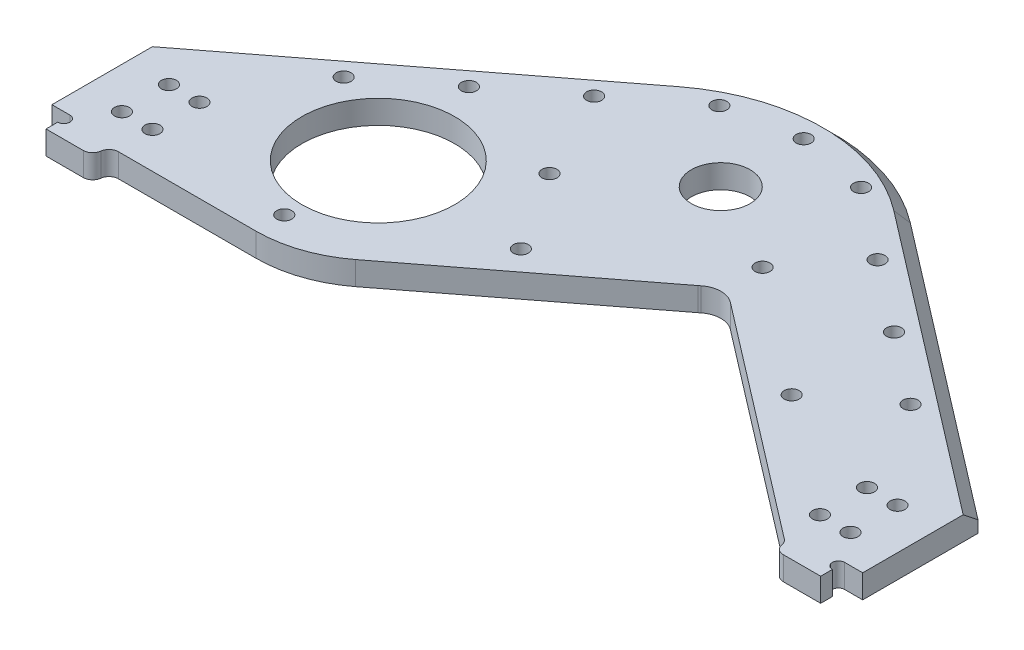
SolidWorks part; units mm, degrees
material "Alum Plate"
ref_plane "Front Plane" through (0, 0, 0) normal (0, 0, 1) x (1, 0, 0)
ref_plane "Top Plane" through (0, 0, 0) normal (0, 1, 0) x (1, 0, 0)
ref_plane "Right Plane" through (0, 0, 0) normal (1, 0, 0) x (0, 0, -1)
sketch "Top Layout" plane through (0, 0, 0) normal (0, 1, 0) x (1, 0, 0)
  line L0 (-114.046, -123.825) -> (-104.775, -123.825) construction
  line L1 (-104.775, -142.875) -> (-101.6, -142.875)
  line L2 (-104.775, -142.875) -> (-104.775, -104.775)
  line L3 (-104.775, -104.775) -> (-101.6, -104.775)
  line L4 (-101.6, -142.875) -> (-101.6, -104.775)
  line L5 (-104.775, -142.875) -> (-101.6, -104.775) construction
  line L6 (-104.775, -104.775) -> (-101.6, -142.875) construction
  line L7 (-19.05, -105.8164) -> (-101.6, -105.8164)
  line L8 (-19.05, -105.8164) -> (-19.05, -141.8336)
  line L9 (-19.05, -141.8336) -> (-101.6, -141.8336)
  line L10 (-101.6, -105.8164) -> (-101.6, -141.8336)
  line L11 (-19.05, -105.8164) -> (-101.6, -141.8336) construction
  line L12 (-19.05, -141.8336) -> (-101.6, -105.8164) construction
  line L13 (-133.096, -85.725) -> (-114.046, -85.725)
  line L14 (-133.096, -85.725) -> (-133.096, -161.925)
  line L15 (-133.096, -161.925) -> (-114.046, -161.925)
  line L16 (-114.046, -85.725) -> (-114.046, -161.925)
  line L17 (-133.096, -85.725) -> (-114.046, -161.925) construction
  line L18 (-133.096, -161.925) -> (-114.046, -85.725) construction
  line L19 (-104.775, -123.825) -> (0, -123.825) construction
  line L20 (0, -123.825) -> (0, 0) construction
  line L21 (-52.3528, -40.1717) -> (0, 0) construction
  line L22 (-70.6449, -16.3328) -> (-18.2922, 23.8388)
  line L23 (-34.0606, -64.0105) -> (18.2922, -23.8388)
  line L24 (-30.9251, 40.3023) -> (-122.2248, -29.7544)
  line L25 (-153.9748, -53.975) -> (-153.9748, -123.825)
  line L26 (-109.5248, -162.052) -> (109.5248, -162.052)
  line L27 (0, -162.052) -> (0, -123.825) construction
  line L28 (-109.5248, -162.052) -> (-109.5248, -20.0093) construction
  line L29 (-104.775, -142.875) -> (-104.775, -152.527)
  line L30 (-104.775, -152.527) -> (104.775, -152.527)
  line L31 (104.775, -104.775) -> (101.6, -104.775)
  line L32 (-144.4498, -73.025) -> (-109.5248, -73.025)
  line L33 (-144.4498, -73.025) -> (-144.4498, -123.825)
  line L34 (-144.4498, -123.825) -> (-109.5248, -123.825) construction
  line L35 (-109.5248, -73.025) -> (-109.5248, -162.052)
  line L36 (-144.4498, -73.025) -> (-109.5248, -123.825) construction
  line L37 (-144.4498, -123.825) -> (-109.5248, -73.025) construction
  line L38 (101.6, -142.875) -> (101.6, -104.775)
  line L39 (104.775, -142.875) -> (101.6, -142.875)
  line L40 (104.775, -142.875) -> (104.775, -104.775)
  line L41 (104.775, -142.875) -> (104.775, -152.527)
  line L42 (109.5248, -162.052) -> (109.5248, -20.0093) construction
  line L43 (30.9251, 40.3023) -> (122.2248, -29.7544)
  line L45 (19.05, -141.8336) -> (101.6, -141.8336)
  line L46 (101.6, -105.8164) -> (101.6, -141.8336)
  line L47 (19.05, -105.8164) -> (101.6, -105.8164)
  line L48 (19.05, -105.8164) -> (19.05, -141.8336)
  line L49 (133.096, -161.925) -> (114.046, -161.925)
  line L50 (114.046, -85.725) -> (114.046, -161.925)
  line L51 (133.096, -85.725) -> (114.046, -85.725)
  line L52 (133.096, -85.725) -> (133.096, -161.925)
  line L53 (144.4498, -123.825) -> (109.5248, -123.825) construction
  line L54 (109.5248, -73.025) -> (109.5248, -162.052)
  line L55 (144.4498, -73.025) -> (109.5248, -73.025)
  line L56 (144.4498, -73.025) -> (144.4498, -123.825)
  line L57 (-109.5248, -123.825) -> (-109.5248, -162.052) construction
  line L62 (-153.9748, -53.975) -> (-122.2248, -53.975)
  line L63 (-122.2248, -53.975) -> (-122.2248, -29.7544)
  line L64 (-144.4498, -123.825) -> (-153.9748, -123.825)
  line L65 (153.9748, -53.975) -> (153.9748, -123.825)
  line L66 (109.5248, -123.825) -> (109.5248, -162.052) construction
  line L67 (144.4498, -123.825) -> (153.9748, -123.825)
  line L68 (122.2248, -29.7544) -> (122.2248, -53.975)
  line L73 (-104.775, -104.775) -> (-104.775, -16.3647) construction
  line L74 (-95.25, -162.052) -> (-95.25, -9.0559) construction
  line L75 (-109.5248, -162.052) -> (-109.5248, -123.825) construction
  line L76 (109.5248, -162.052) -> (109.5248, -123.825) construction
  line L77 (122.2248, -53.975) -> (153.9748, -53.975)
  line L83 (104.775, -155.5496) -> (-104.775, -155.5496) construction
  line L88 (95.25, -162.052) -> (95.25, -9.0559) construction
  line L89 (104.775, -104.775) -> (104.775, -16.3647) construction
  line L92 (-104.775, -152.527) -> (-104.775, -162.052) construction
  line L93 (-14.605, -76.327) -> (14.605, -76.327)
  line L94 (-14.605, -76.327) -> (-14.605, -152.527)
  line L95 (-14.605, -152.527) -> (14.605, -152.527)
  line L96 (14.605, -76.327) -> (14.605, -152.527)
  line L97 (-14.605, -76.327) -> (14.605, -152.527) construction
  line L98 (-14.605, -152.527) -> (14.605, -76.327) construction
  line L99 (104.775, -152.527) -> (104.775, -162.052) construction
  line L100 (-19.05, -105.8164) -> (0, -105.8164) construction
  line L107 (0, -105.8164) -> (19.05, -105.8164) construction
  line L108 (104.775, -123.825) -> (114.046, -123.825) construction
  circle A0 centre (0, 0) radius 114.3
  circle A1 centre (0, 0) radius 7.9375
  circle A2 centre (-52.3528, -40.1717) radius 17.8
  circle A3 centre (0, 0) radius 30.0482
  circle A4 centre (-52.3528, -40.1717) radius 30.0482
  arc A5 (-30.9251, 40.3023) -> (30.9251, 40.3023) centre (0, 0) cw
  point P2 (-103.1875, -123.825)
  point P7 (-60.325, -123.825)
  point P12 (-123.571, -123.825)
  point P30 (-126.9873, -98.425)
  point P35 (0, -114.427)
  point P53 (0, -152.527)
  dimension "D1" = 35.6
  dimension "D2" = 15.875
  dimension "D3" = 228.6
  dimension "D11" = 60.0964
  dimension "D12" = 50.8
  dimension "D14" = 52.5
  dimension "D4" = 3.175
  dimension "D5" = 19.05
  dimension "D6" = 76.2
  dimension "D7" = 82.55
  dimension "D8" = 38.1
  dimension "D9" = 104.775
  dimension "D10" = 18.0086
  dimension "D13" = 9.525
  dimension "D15" = 4.7498
  dimension "D16" = 9.525
  dimension "D17" = 9.652
  dimension "D18" = 50.8
  dimension "D19" = 12.446
  dimension "D20" = 65.9892
  dimension "D21" = 19.05
  dimension "D22" = 34.925
  dimension "D23" = 123.825
  dimension "D24" = 12.7
  dimension "D25" = 9.525
  dimension "D26" = 29.21
  dimension "D27" = 76.2
  dimension "D28" = 3.0226
sketch "Side Layout" plane through (0, 0, 0) normal (1, 0, 0) x (0, 0, -1)
  line L0 (0, -38.1) -> (0, 33.7344) construction
  line L1 (-114.3, -20.955) -> (114.3, -20.955)
  line L2 (-114.3, -20.955) -> (-114.3, -33.655)
  line L3 (-114.3, -33.655) -> (114.3, -33.655)
  line L4 (114.3, -20.955) -> (114.3, -33.655)
  line L5 (-114.3, -20.955) -> (114.3, -33.655) construction
  line L6 (-114.3, -33.655) -> (114.3, -20.955) construction
  line L7 (-9.525, -32.9406) -> (9.525, -32.9406)
  line L8 (-9.525, -32.9406) -> (-9.525, -38.1)
  line L9 (-9.525, -38.1) -> (9.525, -38.1)
  line L10 (9.525, -32.9406) -> (9.525, -38.1)
  line L11 (-9.525, -32.9406) -> (9.525, -38.1) construction
  line L12 (-9.525, -38.1) -> (9.525, -32.9406) construction
  line L13 (-11.9126, -29.3338) -> (11.9126, -29.3338)
  line L14 (-11.9126, -29.3338) -> (-11.9126, -32.9406)
  line L15 (-11.9126, -32.9406) -> (11.9126, -32.9406)
  line L16 (11.9126, -29.3338) -> (11.9126, -32.9406)
  line L17 (-11.9126, -29.3338) -> (11.9126, -32.9406) construction
  line L18 (-11.9126, -32.9406) -> (11.9126, -29.3338) construction
  line L19 (-6.35, -32.9406) -> (6.35, -32.9406)
  line L20 (-6.35, -32.9406) -> (-6.35, 33.7344)
  line L21 (-6.35, 33.7344) -> (6.35, 33.7344)
  line L22 (6.35, -32.9406) -> (6.35, 33.7344)
  line L23 (-6.35, -32.9406) -> (6.35, 33.7344) construction
  line L24 (-6.35, 33.7344) -> (6.35, -32.9406) construction
  line L25 (-162.052, 0) -> (-123.825, 0) construction
  line L26 (114.3, -33.655) -> (114.3, 0) construction
  line L27 (-142.875, 19.05) -> (-104.775, 19.05)
  line L28 (-40.1717, -9.525) -> (-40.1717, 5.4) construction
  line L29 (-142.875, 19.05) -> (-142.875, -19.05)
  line L30 (-142.875, -19.05) -> (-104.775, -19.05)
  line L31 (-104.775, 19.05) -> (-104.775, -19.05)
  line L32 (-142.875, 19.05) -> (-104.775, -19.05) construction
  line L33 (-142.875, -19.05) -> (-104.775, 19.05) construction
  line L34 (-130.175, -38.1) -> (-117.9516, -38.1) construction
  line L35 (-57.9717, -14.6) -> (-22.3717, -14.6)
  line L36 (-30.0482, -2.794) -> (30.0482, -2.794)
  line L37 (-30.0482, -2.794) -> (-30.0482, -20.955)
  line L38 (-30.0482, -20.955) -> (30.0482, -20.955)
  line L39 (30.0482, -2.794) -> (30.0482, -20.955)
  line L40 (-30.0482, -2.794) -> (30.0482, -20.955) construction
  line L41 (-30.0482, -20.955) -> (30.0482, -2.794) construction
  line L42 (-30.0482, -2.794) -> (-30.0482, 0) construction
  line L43 (-123.825, 0) -> (0, 0) construction
  line L44 (-57.9717, -14.6) -> (-57.9717, 25.4)
  line L45 (-57.9717, 25.4) -> (-22.3717, 25.4)
  line L46 (-22.3717, -14.6) -> (-22.3717, 25.4)
  line L47 (-19.05, 0) -> (19.05, 0)
  line L48 (-19.05, 0) -> (-19.05, -1.9812)
  line L49 (-19.05, -1.9812) -> (19.05, -1.9812)
  line L50 (19.05, 0) -> (19.05, -1.9812)
  line L51 (-19.05, 0) -> (19.05, -1.9812) construction
  line L52 (-19.05, -1.9812) -> (19.05, 0) construction
  line L53 (-70.2199, -3.175) -> (-10.1235, -3.175)
  line L54 (-70.2199, -3.175) -> (-70.2199, -15.875)
  line L55 (-70.2199, -15.875) -> (-10.1235, -15.875)
  line L56 (-10.1235, -3.175) -> (-10.1235, -15.875)
  line L57 (-70.2199, -3.175) -> (-10.1235, -15.875) construction
  line L58 (-70.2199, -15.875) -> (-10.1235, -3.175) construction
  line L59 (-40.1717, -9.525) -> (-40.1717, 0) construction
  line L60 (-57.9717, -14.6) -> (-22.3717, 25.4) construction
  line L61 (-57.9717, 25.4) -> (-22.3717, -14.6) construction
  line L62 (-22.3717, 0) -> (-57.9717, 0) construction
  line L63 (-137.8162, 0) -> (-123.825, -13.9912) construction
  line L64 (-139.065, 15.24) -> (-108.585, 15.24) construction
  line L65 (-139.065, 15.24) -> (-139.065, -15.24) construction
  line L66 (-139.065, -15.24) -> (-108.585, -15.24) construction
  line L67 (-108.585, 15.24) -> (-108.585, -15.24) construction
  line L68 (-139.065, 15.24) -> (-108.585, -15.24) construction
  line L69 (-139.065, -15.24) -> (-108.585, 15.24) construction
  line L70 (-137.8162, 0) -> (-123.825, 13.9912) construction
  line L71 (-123.825, -13.9912) -> (-109.8338, 0) construction
  line L72 (-123.825, 13.9912) -> (-109.8338, 0) construction
  line L73 (-137.8162, 0) -> (-109.8338, 0) construction
  line L74 (-123.825, -13.9912) -> (-123.825, 13.9912) construction
  line L75 (-6.35, 17.8594) -> (6.35, 17.8594)
  line L76 (114.3, 0) -> (-114.3, 0) construction
  line L77 (-22.3717, 19.05) -> (-6.35, 19.05) construction
  line L78 (-123.825, 38.1) -> (-97.9206, 38.1) construction
  line L79 (-19.05, -3.5814) -> (19.05, -3.5814)
  line L80 (-19.05, -3.5814) -> (-19.05, -1.9812)
  line L81 (-19.05, -1.9812) -> (19.05, -1.9812)
  line L82 (19.05, -3.5814) -> (19.05, -1.9812)
  line L83 (-19.05, -3.5814) -> (19.05, -1.9812) construction
  line L84 (-19.05, -1.9812) -> (19.05, -3.5814) construction
  line L85 (-8.7376, -16.7608) -> (8.7376, -16.7608)
  line L86 (-8.7376, -16.7608) -> (-8.7376, -29.3338)
  line L87 (-8.7376, -29.3338) -> (8.7376, -29.3338)
  line L88 (8.7376, -16.7608) -> (8.7376, -29.3338)
  line L89 (-8.7376, -16.7608) -> (8.7376, -29.3338) construction
  line L90 (-8.7376, -29.3338) -> (8.7376, -16.7608) construction
  line L91 (-8.7376, -3.5814) -> (8.7376, -3.5814)
  line L92 (-8.7376, -3.5814) -> (-8.7376, -16.1544)
  line L93 (-8.7376, -16.1544) -> (8.7376, -16.1544)
  line L94 (8.7376, -3.5814) -> (8.7376, -16.1544)
  line L95 (-8.7376, -3.5814) -> (8.7376, -16.1544) construction
  line L96 (-8.7376, -16.1544) -> (8.7376, -3.5814) construction
  circle A0 centre (-123.825, 0) radius 18.0086
  circle A1 centre (-123.825, 0) radius 38.1
  circle A2 centre (-139.065, 15.24) radius 1.905
  circle A3 centre (-108.585, 15.24) radius 1.905
  circle A4 centre (-108.585, -15.24) radius 1.905
  circle A5 centre (-139.065, -15.24) radius 1.905
  circle A6 centre (-137.8162, 0) radius 1.6002
  circle A7 centre (-123.825, 13.9912) radius 1.6002
  circle A8 centre (-109.8338, 0) radius 1.6002
  circle A9 centre (-123.825, -13.9912) radius 1.6002
  point P0 (0, -27.305)
  point P6 (0, -31.1372)
  point P7 (0, -35.5203)
  point P21 (0, 0.3969)
  point P32 (0, -11.8745)
  point P43 (0, -0.9906)
  point P55 (-40.1717, -9.525)
  point P72 (-40.1717, 5.4)
  point P88 (0, -23.0473)
  point P93 (0, -2.7813)
  point P102 (0, -9.8679)
  dimension "D17" = 3.81
  dimension "D18" = 3.2004
  dimension "D1" = 12.7
  dimension "D2" = 5.1594
  dimension "D3" = 19.05
  dimension "D4" = 3.6068
  dimension "D5" = 23.8252
  dimension "D6" = 12.7
  dimension "D7" = 18.161
  dimension "D8" = 1.9812
  dimension "D9" = 12.7
  dimension "D10" = 40
  dimension "D11" = 25.4
  dimension "D12" = 50.8
  dimension "D13" = 41.275
  dimension "D14" = 30.48
  dimension "D15" = 4.445
  dimension "D16" = 19.7866
  dimension "D19" = 15.875
  dimension "D20" = 6.35
  dimension "D21" = 38.1
  dimension "D22" = 1.6002
  dimension "D23" = 38.1
  dimension "D24" = 17.4752
  dimension "D25" = 12.573
ref_plane "Plane1" through (0, 25.4, 0) normal (0, 1, 0) x (1, 0, 0)
sketch "Sketch3" plane through (0, 25.4, 0) normal (0, 1, 0) x (1, 0, 0)
  line L0 (-104.775, -36.3747) -> (-30.9251, 20.2924)
  line L1 (-104.775, -104.775) -> (-104.775, -16.3647) construction
  line L2 (0, -200130.175) -> (0, 199882.0484) construction
  line L3 (-30.9251, 40.3023) -> (-122.2248, -29.7544) construction
  line L5 (-104.775, -36.3747) -> (-104.775, -77.6497)
  line L6 (-92.075, -77.6497) -> (-104.775, -77.6497)
  line L7 (30.9251, 20.2924) -> (104.775, -36.3747)
  line L8 (104.775, -77.6497) -> (92.075, -77.6497)
  line L9 (104.775, -36.3747) -> (104.775, -77.6497)
  line L11 (104.775, -104.775) -> (104.775, -16.3647) construction
  line L12 (30.9251, 40.3023) -> (122.2248, -29.7544) construction
  line L13 (92.075, -74.6536) -> (24.1423, -22.5271)
  line L14 (-32.2514, -66.3682) -> (20.1013, -26.1965)
  line L15 (-30.9251, 20.2924) -> (0, 44.022)
  line L16 (0, 44.022) -> (30.9251, 20.2924)
  line L17 (-92.075, -77.6497) -> (-92.075, -73.1917)
  line L19 (-92.075, -73.1917) -> (-52.3528, -73.1917)
  line L20 (92.075, -74.6536) -> (92.075, -77.6497)
  circle A0 centre (-52.3528, -40.1717) radius 17.8 construction
  circle A1 centre (-52.3528, -40.1717) radius 17.8
  circle A2 centre (0, 0) radius 7.9375
  circle A3 centre (0, 0) radius 7.9375 construction
  arc A4 (-52.3528, -73.1917) -> (-32.2514, -66.3682) centre (-52.3528, -40.1717) ccw
  arc A5 (20.1013, -26.1965) -> (24.1423, -22.5271) centre (0, 0) ccw
  arc A6 (30.9251, 20.2924) -> (-30.9251, 20.2924) centre (0, -20.01) ccw construction
  point P28 (0, 44.022)
  dimension "D1" = 33.02
  dimension "D5" = 50.8
  dimension "D2" = 41.275
  dimension "D3" = 34.925
  dimension "D4" = 12.7
  dimension "D6" = 38.1
extrude "Boss-Extrude1" add sketch "Sketch3" against normal blind 6.35
sketch "Sketch7" plane through (0, 25.4, 0) normal (0, 1, 0) x (1, 0, 0)
  circle A0 centre (-52.3528, -40.1717) radius 20.6375
  dimension "D1" = 41.275
extrude "Cut-Extrude1" cut sketch "Sketch7" against normal through all
sketch "Sketch8" plane through (0, 25.4, 0) normal (0, 1, 0) x (1, 0, 0)
  line L0 (-109.5248, -162.052) -> (-109.5248, -20.0093) construction
  line L1 (-104.775, -77.6497) -> (-109.5248, -77.6497)
  line L2 (-104.775, -77.6497) -> (-104.775, -36.3747)
  line L3 (-104.775, -36.3747) -> (-109.5248, -36.3747)
  line L4 (-109.5248, -77.6497) -> (-109.5248, -36.3747)
  line L5 (-104.775, -77.6497) -> (-109.5248, -36.3747) construction
  line L6 (-104.775, -36.3747) -> (-109.5248, -77.6497) construction
  line L7 (104.775, -77.6497) -> (109.5248, -77.6497)
  line L8 (104.775, -77.6497) -> (104.775, -36.3747)
  line L9 (104.775, -36.3747) -> (109.5248, -36.3747)
  line L10 (109.5248, -77.6497) -> (109.5248, -36.3747)
  line L11 (104.775, -77.6497) -> (109.5248, -36.3747) construction
  line L12 (104.775, -36.3747) -> (109.5248, -77.6497) construction
  point P4 (-107.1499, -57.0122)
  point P10 (107.1499, -57.0122)
extrude "Boss-Extrude4" add sketch "Sketch8" against normal through all
sketch "Sketch10" plane through (0, 25.4, 0) normal (0, 1, 0) x (1, 0, 0)
  line L0 (0, 33.4567) -> (0, 30.79) construction
  line L1 (-5.1026, 40.1066) -> (0, 33.4567) construction
  line L2 (0, 33.4567) -> (5.1026, 40.1066) construction
  line L3 (0, 44.022) -> (-104.775, -36.3747) construction
  line L4 (104.775, -36.3747) -> (0, 44.022) construction
  circle A0 centre (0, 33.4567) radius 4.7625 construction
  circle A1 centre (0, 33.4567) radius 2.0193
  arc A3 (30.9251, 20.2924) -> (-30.9251, 20.2924) centre (0, -20.01) ccw construction
  dimension "D2" = 9.525
  dimension "D3" = 4.0386
  dimension "D1" = 8.382
extrude "Spacer Holes" cut sketch "Sketch10" against normal through all
pattern_linear "Spacer Hole Pattern" count 5 spacing 24.13 along (-0.7934, 0, 0.6088) of "Spacer Holes"
mirror "Spacer Hole Mirror" about plane through (0, 0, 0) normal (1, 0, 0) of "Spacer Hole Pattern"
sketch "Sketch16" plane through (0, 25.4, 0) normal (0, 1, 0) x (1, 0, 0)
  line L0 (-109.5248, -50.6622) -> (-98.425, -50.6622) construction
  line L1 (-109.5248, -36.3747) -> (-109.5248, -77.6497) construction
  line L2 (-98.425, -50.6622) -> (-98.425, -63.3622) construction
  line L3 (-98.425, -63.3622) -> (-109.5248, -63.3622) construction
  line L4 (-98.425, -63.3622) -> (-98.425, -77.6497) construction
  line L5 (-109.5248, -77.6497) -> (-92.075, -77.6497) construction
  line L6 (-98.425, -50.6622) -> (-98.425, -36.3747) construction
  line L7 (-104.775, -36.3747) -> (-109.5248, -36.3747) construction
  line L8 (-104.775, -36.3747) -> (-104.775, -77.6497) construction
  line L9 (0, 0) -> (0, 30.79) construction
  line L10 (104.775, -36.3747) -> (104.775, -77.6497) construction
  circle A0 centre (-98.425, -50.6622) radius 2.0193
  circle A1 centre (-98.425, -63.3622) radius 2.0193
  circle A4 centre (98.425, -63.3622) radius 2.0193
  circle A5 centre (98.425, -50.6622) radius 2.0193
  arc A6 (30.9251, 20.2924) -> (-30.9251, 20.2924) centre (0, -20.01) ccw construction
  dimension "D1" = 4.0386
  dimension "D2" = 12.7
  dimension "D3" = 6.35
extrude "Custom Nutstrip Holes" cut sketch "Sketch16" against normal through all
sketch "Sketch36" plane through (0, 25.4, 0) normal (0, 1, 0) x (1, 0, 0)
  line L0 (-52.3528, -65.5717) -> (-12.44, -41.5615) construction
  line L1 (-12.44, -41.5615) -> (24.5129, -13.2066) construction
  line L2 (24.5129, -13.2066) -> (58.2939, -39.1277) construction
  line L3 (-32.2514, -66.3682) -> (20.1013, -26.1965) construction
  line L4 (24.1423, -22.5271) -> (92.075, -74.6536) construction
  line L5 (-12.44, -41.5615) -> (-7.8012, -47.6069) construction
  line L6 (58.2939, -39.1277) -> (53.6552, -45.1731) construction
  line L7 (-52.3528, -65.5717) -> (-52.3528, -40.1717) construction
  line L8 (58.2939, -39.1277) -> (92.075, -65.0488) construction
  line L9 (92.075, -65.0488) -> (92.075, -77.6497) construction
  line L10 (-52.3528, -40.1717) -> (-26.1764, -20.0858) construction
  line L11 (-26.1764, -20.0858) -> (0, 0) construction
  line L12 (92.075, -74.6536) -> (92.075, -77.6497) construction
  circle A0 centre (-52.3528, -65.5717) radius 2.0193
  circle A1 centre (58.2939, -39.1277) radius 2.0193
  circle A2 centre (24.5129, -13.2066) radius 2.0193
  circle A3 centre (-12.44, -41.5615) radius 2.0193
  circle A4 centre (-76.5745, -25.3009) radius 2.0193 construction
  circle A5 centre (-52.3528, -65.5717) radius 4.7625 construction
  circle A6 centre (-12.44, -41.5615) radius 4.7625 construction
  circle A7 centre (24.5129, -13.2066) radius 4.7625 construction
  circle A8 centre (58.2939, -39.1277) radius 4.7625 construction
  arc A9 (-52.3528, -73.1917) -> (-32.2514, -66.3682) centre (-52.3528, -40.1717) ccw construction
  circle A10 centre (-26.1764, -20.0858) radius 2.0193
  dimension "D1" = 9.525
  dimension "D2" = 25.4
  dimension "D3" = 7.62
extrude "Aux Spacer Holes" cut sketch "Sketch36" against normal through all
sketch "Sketch58" plane through (0, 25.4, 0) normal (0, 1, 0) x (1, 0, 0)
  line L0 (0, 22.408) -> (0, 30.79) construction
  line L1 (-30.9251, 20.2924) -> (0, 44.022)
  line L2 (0, 44.022) -> (30.9251, 20.2924)
  circle A0 centre (0, 22.408) radius 2.0193
  arc A1 (30.9251, 20.2924) -> (-30.9251, 20.2924) centre (0, -20.01) ccw construction
  circle A2 centre (19.1436, 18.7673) radius 2.0193 construction
  arc A4 (-30.9251, 20.2924) -> (30.9251, 20.2924) centre (0, -20.01) cw
  dimension "D1" = 8.382
extrude "Cut-Extrude30" cut sketch "Sketch58" against normal through all
sketch "Sketch11" plane through (0, 25.4, 0) normal (0, 1, 0) x (1, 0, 0)
  circle A0 centre (0, 22.408) radius 2.4892
  circle A1 centre (-76.5745, -25.3009) radius 2.4892
  circle A2 centre (-57.4308, -10.6115) radius 2.4892
  circle A3 centre (-38.2872, 4.0779) radius 2.4892
  circle A4 centre (-19.1436, 18.7673) radius 2.4892
  circle A5 centre (19.1436, 18.7673) radius 2.4892
  circle A6 centre (38.2872, 4.0779) radius 2.4892
  circle A7 centre (57.4308, -10.6115) radius 2.4892
  circle A8 centre (76.5745, -25.3009) radius 2.4892
  circle A10 centre (-52.3528, -65.5717) radius 2.4892
  circle A11 centre (-98.425, -50.6622) radius 2.4892
  circle A12 centre (-98.425, -63.3622) radius 2.4892
  circle A13 centre (98.425, -50.6622) radius 2.4892
  circle A14 centre (98.425, -63.3622) radius 2.4892
  circle A16 centre (-26.1764, -20.0858) radius 2.4892
  circle A17 centre (-12.44, -41.5615) radius 2.4892
  circle A18 centre (24.5129, -13.2066) radius 2.4892
  circle A19 centre (58.2939, -39.1277) radius 2.4892
  dimension "D1" = 4.9784
sketch "Sketch84" plane through (0, 25.4, 0) normal (0, 1, 0) x (1, 0, 0)
  line L0 (-98.425, -50.6622) -> (-90.17, -50.6622) construction
  line L1 (-98.425, -63.3622) -> (-90.17, -63.3622) construction
  line L2 (98.425, -63.3622) -> (90.17, -63.3622) construction
  line L3 (98.425, -50.6622) -> (90.17, -50.6622) construction
  circle A4 centre (90.17, -50.6622) radius 2.0193
  circle A5 centre (90.17, -63.3622) radius 2.0193
  circle A6 centre (-90.17, -50.6622) radius 2.0193
  circle A7 centre (-90.17, -63.3622) radius 2.0193
  circle A8 centre (-98.425, -50.6622) radius 2.0193 construction
  dimension "D1" = 8.255
extrude "Cut-Extrude40" cut sketch "Sketch84" against normal through all
sketch "Sketch75" plane through (0, 25.4, 0) normal (0, 1, 0) x (1, 0, 0)
  line L0 (-104.775, -36.3747) -> (-109.5248, -40.0193)
  line L1 (-109.5248, -36.3747) -> (-109.5248, -77.6497) construction
  line L2 (-109.5248, -40.0193) -> (-109.5248, -36.3747)
  line L3 (-109.5248, -36.3747) -> (-104.775, -36.3747)
  line L4 (104.775, -36.3747) -> (109.5248, -40.0193)
  line L5 (109.5248, -77.6497) -> (109.5248, -36.3747) construction
  line L6 (109.5248, -40.0193) -> (109.5248, -36.3747)
  line L7 (109.5248, -36.3747) -> (104.775, -36.3747)
  line L8 (104.775, -36.3747) -> (30.9251, 20.2924) construction
  line L9 (-30.9251, 20.2924) -> (-104.775, -36.3747) construction
extrude "Cut-Extrude34" cut sketch "Sketch75" against normal through all
sketch "Sketch105" plane through (0, 25.4, 0) normal (0, 1, 0) x (1, 0, 0)
  line L1 (-109.5248, -77.6497) -> (-104.648, -77.6497)
  line L2 (-109.5248, -77.6497) -> (-109.5248, -71.1727)
  line L3 (-109.5248, -71.1727) -> (-104.648, -71.1727)
  line L4 (-104.648, -77.6497) -> (-104.648, -71.1727)
  line L5 (-109.5248, -77.6497) -> (-104.648, -71.1727) construction
  line L6 (-109.5248, -71.1727) -> (-104.648, -77.6497) construction
  line L7 (109.5248, -77.6497) -> (104.648, -77.6497)
  line L8 (109.5248, -77.6497) -> (109.5248, -71.1727)
  line L9 (109.5248, -71.1727) -> (104.648, -71.1727)
  line L10 (104.648, -77.6497) -> (104.648, -71.1727)
  line L11 (109.5248, -77.6497) -> (104.648, -71.1727) construction
  line L12 (109.5248, -71.1727) -> (104.648, -77.6497) construction
  point P4 (-107.0864, -74.4112)
  point P10 (107.0864, -74.4112)
  dimension "D1" = 6.477
  dimension "D2" = 4.8768
extrude "Cut-Extrude54" cut sketch "Sketch105" against normal through all
sketch "Sketch106" plane through (0, 25.4, 0) normal (0, 1, 0) x (1, 0, 0)
  line L0 (-104.648, -77.6497) -> (-104.648, -71.1727) construction
  line L1 (104.648, -71.1727) -> (104.648, -77.6497) construction
  circle A0 centre (-104.648, -72.8237) radius 1.651
  circle A1 centre (104.648, -72.8237) radius 1.651
  dimension "D1" = 3.302
extrude "Cut-Extrude55" cut sketch "Sketch106" against normal through all
chamfer "Chamfer5" distance 3.175 angle 45 3 edges at (70.2249, 25.4, 9.8635) (-70.2249, 25.4, 9.8635) (0, 25.4, -30.79)
sketch "Sketch89" plane through (0, 25.4, 0) normal (0, 1, 0) x (1, 0, 0)
  circle A0 centre (0, 0) radius 19.8501
  circle A1 centre (0, 0) radius 12.7254
  circle A2 centre (0, 0) radius 11.9126
  circle A3 centre (0, 0) radius 6.3754
  dimension "D1" = 39.7002
  dimension "D2" = 25.4508
  dimension "D3" = 23.8252
  dimension "D4" = 12.7508
fillet "Fillet21" radius 6.35 1 edges at (24.1423, 22.225, 22.5271)
fillet "Fillet22" radius 2.54 2 edges at (92.075, 22.225, 74.6536) (-92.075, 22.225, 73.1917)
fillet "Fillet23" radius 2.54 2 edges at (92.075, 22.225, 77.6497) (-92.075, 22.225, 77.6497)
